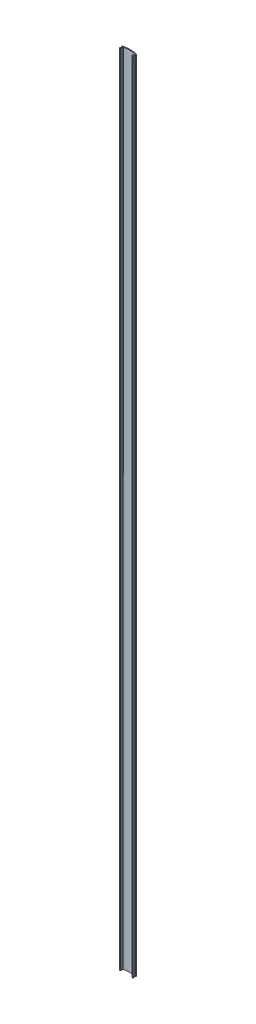
SolidWorks part; units mm, degrees
ref_plane "Alzado" through (0, 0, 0) normal (0, 0, 1) x (1, 0, 0)
ref_plane "Planta" through (0, 0, 0) normal (0, 1, 0) x (1, 0, 0)
ref_plane "Vista lateral" through (0, 0, 0) normal (1, 0, 0) x (0, 0, -1)
sketch "Croquis1" plane through (0, 0, 0) normal (0, 1, 0) x (1, 0, 0)
  line L1 (-27.0457, 0.111) -> (-27.0457, -0.971)
  line L5 (-11.9805, -2.2021) -> (-12.6657, -2.2021)
  line L6 (-12.9657, 0.111) -> (-12.9657, -1.9021)
  line L7 (-12.0057, 0.111) -> (-12.0057, -0.971)
  line L9 (-26.0857, 0.111) -> (-26.0857, -1.9021)
  line L10 (-27.0709, -2.2021) -> (-26.3857, -2.2021)
  arc A0 (-13.1826, 0.7215) -> (-25.8689, 0.7215) centre (-19.5257, -25.4179) ccw
  arc A1 (-11.4042, 1.3586) -> (-27.6472, 1.3586) centre (-19.5257, -28.5618) ccw
  arc A4 (-27.2607, -1.2224) -> (-27.0709, -2.2021) centre (-27.1832, -1.7156) ccw
  arc A9 (-27.2637, 0.3629) -> (-27.8844, 1.0543) centre (-27.1597, 1.0805) cw
  arc A17 (-11.167, 1.0543) -> (-11.4042, 1.3586) centre (-11.4668, 1.0652) ccw
  arc A18 (-12.9392, 0.3634) -> (-13.1826, 0.7215) centre (-13.2327, 0.4257) ccw
  arc A19 (-27.0457, -0.971) -> (-27.2607, -1.2224) centre (-27.3002, -0.971) cw
  arc A20 (-12.9392, 0.3634) -> (-12.9657, 0.111) centre (-11.7513, 0.111) ccw
  arc A21 (-12.9657, -1.9021) -> (-12.6657, -2.2021) centre (-12.6657, -1.9021) ccw
  arc A22 (-27.2637, 0.3629) -> (-27.0457, 0.111) centre (-27.3002, 0.111) cw
  arc A23 (-11.7877, 0.3629) -> (-12.0057, 0.111) centre (-11.7513, 0.111) ccw
  arc A24 (-12.0057, -0.971) -> (-11.7907, -1.2224) centre (-11.7513, -0.971) ccw
  arc A25 (-11.7877, 0.3629) -> (-11.167, 1.0543) centre (-11.8917, 1.0805) ccw
  arc A26 (-11.7907, -1.2224) -> (-11.9805, -2.2021) centre (-11.8682, -1.7156) cw
  arc A27 (-26.0857, -1.9021) -> (-26.3857, -2.2021) centre (-26.3857, -1.9021) cw
  arc A28 (-26.1122, 0.3634) -> (-26.0857, 0.111) centre (-27.3002, 0.111) cw
  arc A29 (-26.1122, 0.3634) -> (-25.8689, 0.7215) centre (-25.8188, 0.4257) cw
  arc A30 (-27.8844, 1.0543) -> (-27.6472, 1.3586) centre (-27.5846, 1.0652) cw
  dimension "D5" = 0.3
  dimension "D6" = 0.3
extrude "Saliente-Extruir1" add sketch "Croquis1" along normal blind 920
